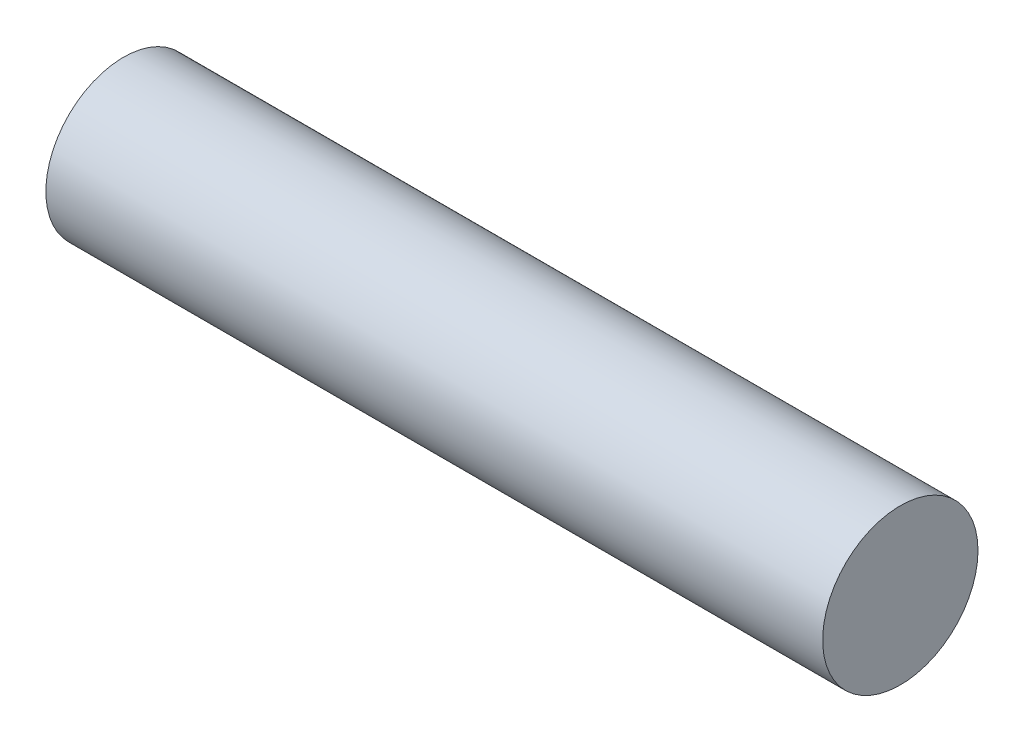
SolidWorks part; units mm, degrees
material "Ti-5Al-2.5Sn Annealed (SS)"
ref_plane "Front Plane" through (0, 0, 0) normal (0, 0, 1) x (1, 0, 0)
ref_plane "Top Plane" through (0, 0, 0) normal (0, 1, 0) x (1, 0, 0)
ref_plane "Right Plane" through (0, 0, 0) normal (1, 0, 0) x (0, 0, -1)
sketch "RivetProfile" plane through (0, 0, 0) normal (1, 0, 0) x (0, 0, -1)
  circle A0 centre (0, 0) radius 40
  dimension "D1" = 80
extrude "Boss-Extrude1" add sketch "RivetProfile" along normal blind 400 contours A0
equation "\"D1@RivetProfile\" = \"HoleMountDiameter@PrintingPress.Assembly\""
equation "\"D1@Boss-Extrude1\"= 4 * \"RivetLength@PrintingPress.Assembly\""
